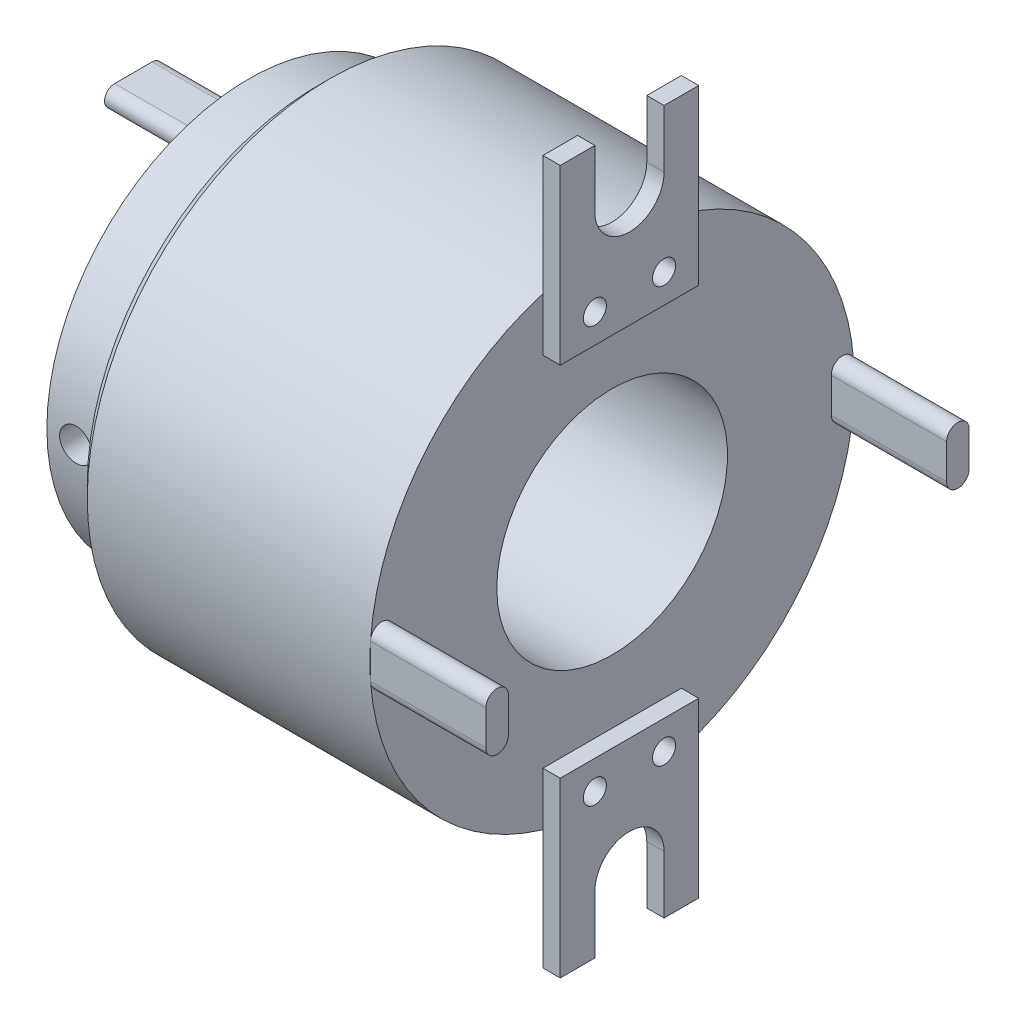
SolidWorks part; units mm, degrees
ref_plane "Front" through (0, 0, 0) normal (0, 0, 1) x (1, 0, 0)
ref_plane "Top" through (0, 0, 0) normal (0, 1, 0) x (1, 0, 0)
ref_plane "Right" through (0, 0, 0) normal (1, 0, 0) x (0, 0, -1)
sketch "Sketch1" plane through (0, 0, 0) normal (0, 0, 1) x (1, 0, 0)
  line L0 (-13.0276, 0) -> (13.0276, 0) construction
  line L1 (-13.0276, 10) -> (18.4724, 10)
  line L2 (18.4724, 10) -> (18.4724, 21)
  line L3 (18.4724, 21) -> (-7.0276, 21)
  line L4 (-7.0276, 21) -> (-7.0276, 15.5)
  line L5 (-7.0276, 15.5) -> (-8.0276, 15.5)
  line L6 (-8.0276, 15.5) -> (-8.0276, 17.5)
  line L7 (-8.0276, 17.5) -> (-13.0276, 17.5)
  line L8 (-13.0276, 17.5) -> (-13.0276, 10)
  point P4 (0, 0)
  dimension "D1" = 6
  dimension "D2" = 1
  dimension "D3" = 10
  dimension "D4" = 21
  dimension "D5" = 17.5
  dimension "D6" = 2
  dimension "D7" = 25.5
revolve "Revolve1" add sketch "Sketch1" angle 360 about L0
ref_plane "Plane1" through (0, 0, 17.5) normal (0, 0, 1) x (1, 0, 0)
sketch "Sketch2" plane through (0, 0, 17.5) normal (0, 0, 1) x (1, 0, 0)
  line L0 (-10.5276, 0) -> (0, 0) construction
  line L1 (-13.0276, 17.5) -> (-13.0276, -17.5) construction
  circle A0 centre (-10.5276, 0) radius 1.4
  point P6 (-10.5276, 0)
  dimension "D2" = 2.8
  dimension "D1" = 2.5
extrude "Cut-Extrude1" cut sketch "Sketch2" against normal blind 10 contours A0
pattern_circular "CirPattern1" count 2 over 360 about axis through (-10.5276, 0, 0) along (0, 0, 1) of "Cut-Extrude1"
chamfer "Chamfer1" distance 1 angle 45 1 edges at (-7.0276, 0, 21)
sketch "Sketch5" plane through (-13.0276, 0, 0) normal (-1, 0, 0) x (0, 0, 1)
  line L0 (0, 0) -> (0, 12.077) construction
  line L1 (-1.6223, 12.077) -> (1.6223, 12.077) construction
  line L2 (-1.6223, 12.9582) -> (1.6223, 12.9582)
  line L3 (-1.6223, 11.1958) -> (1.6223, 11.1958)
  line L4 (1.6223, -12.077) -> (-1.6223, -12.077) construction
  line L5 (1.6223, -12.9582) -> (-1.6223, -12.9582)
  line L6 (1.6223, -11.1958) -> (-1.6223, -11.1958)
  circle A0 centre (0, 0) radius 15.5 construction
  arc A1 (-1.6223, 12.9582) -> (-1.6223, 11.1958) centre (-1.6223, 12.077) ccw
  circle A3 centre (0, 0) radius 15.5 construction
  arc A4 (1.6223, 11.1958) -> (1.6223, 12.9582) centre (1.6223, 12.077) ccw
  arc A5 (1.6223, -12.9582) -> (1.6223, -11.1958) centre (1.6223, -12.077) ccw
  arc A6 (-1.6223, -11.1958) -> (-1.6223, -12.9582) centre (-1.6223, -12.077) ccw
  point P6 (0, 12.077)
  point P16 (0, -12.077)
  dimension "D1" = 2
extrude "Boss-Extrude1" add sketch "Sketch5" along normal blind 10
sketch "Sketch6" plane through (18.4724, 0, 0) normal (1, 0, 0) x (0, 0, -1)
  line L0 (0, 0) -> (-19.9681, 0) construction
  line L1 (-19.9681, -1.5052) -> (-19.9681, 1.5052) construction
  line L2 (-20.9433, -1.5052) -> (-20.9433, 1.5052)
  line L3 (-18.9929, -1.5052) -> (-18.9929, 1.5052)
  line L4 (18.9929, 1.5052) -> (18.9929, -1.5052)
  line L5 (20.9433, 1.5052) -> (20.9433, -1.5052)
  line L6 (19.9681, 1.5052) -> (19.9681, -1.5052) construction
  arc A0 (-20.9433, -1.5052) -> (-18.9929, -1.5052) centre (-19.9681, -1.5052) ccw
  arc A1 (-18.9929, 1.5052) -> (-20.9433, 1.5052) centre (-19.9681, 1.5052) ccw
  circle A2 centre (0, 0) radius 21 construction
  arc A3 (20.9433, 1.5052) -> (18.9929, 1.5052) centre (19.9681, 1.5052) ccw
  arc A4 (18.9929, -1.5052) -> (20.9433, -1.5052) centre (19.9681, -1.5052) ccw
  point P5 (-19.9681, 0)
  point P16 (19.9681, 0)
  dimension "D1" = 2
extrude "Boss-Extrude2" add sketch "Sketch6" along normal blind 10
sketch "Sketch7" plane through (18.4724, 0, 0) normal (1, 0, 0) x (0, 0, -1)
  line L0 (0, 0) -> (0, 23) construction
  line L1 (-3, 18) -> (3, 18) construction
  line L2 (-6, 30.5) -> (-3, 30.5)
  line L3 (-6, 30.5) -> (-6, 15.5)
  line L4 (-6, 15.5) -> (6, 15.5)
  line L5 (6, 30.5) -> (6, 15.5)
  line L6 (-6, 30.5) -> (6, 15.5) construction
  line L7 (-6, 15.5) -> (6, 30.5) construction
  line L8 (-3, 25.5) -> (-3, 30.5)
  line L9 (3, 25.5) -> (3, 30.5)
  line L10 (3, 30.5) -> (6, 30.5)
  circle A0 centre (-3, 18) radius 1
  circle A1 centre (3, 18) radius 1
  arc A2 (-3, 25.5) -> (3, 25.5) centre (0, 25.5) ccw
  point P10 (0, 18)
  point P13 (0, 0)
  point P18 (0, 22.5)
  dimension "D6" = 2
  dimension "D1" = 15
  dimension "D2" = 30.5
  dimension "D3" = 12
  dimension "D4" = 18
  dimension "D5" = 6
  dimension "D7" = 22.5
  dimension "D8" = 6
extrude "Boss-Extrude3" add sketch "Sketch7" along normal blind 1.5
pattern_circular "CirPattern2" count 2 over 360 about axis through (0, 0, 0) along (1, 0, 0) of "Boss-Extrude3"
